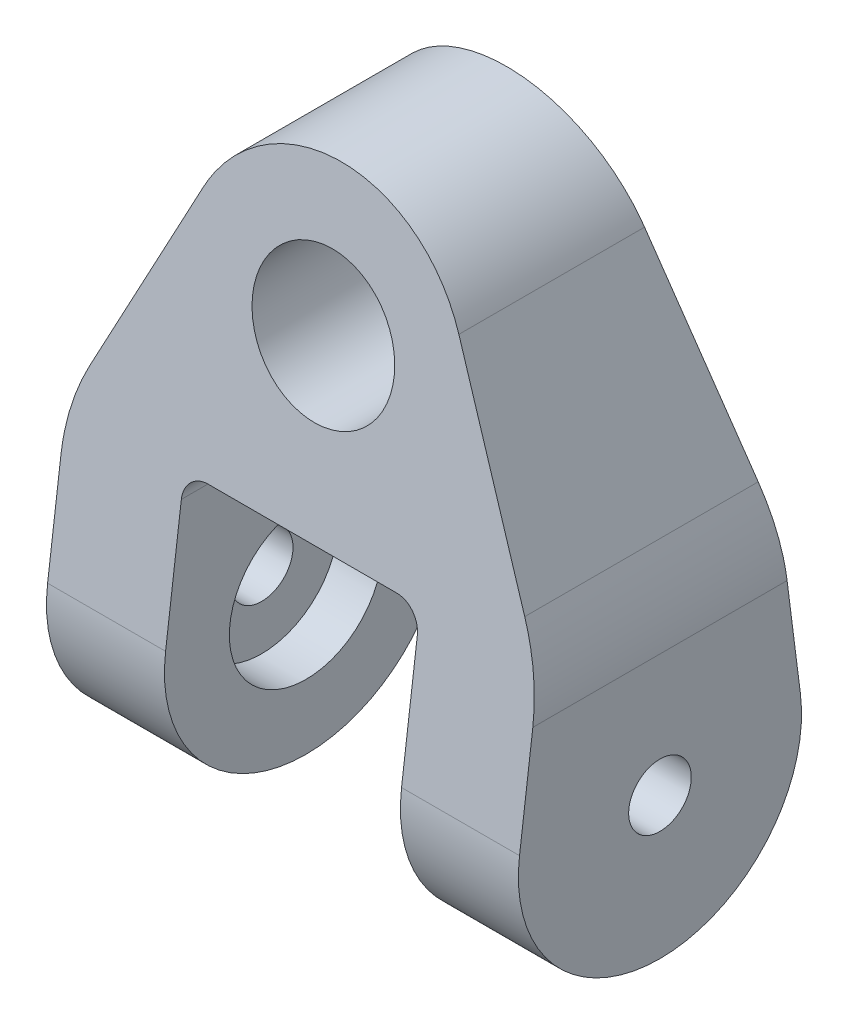
SolidWorks part; units mm, degrees
ref_plane "Front Plane" through (0, 0, 0) normal (0, 0, 1) x (1, 0, 0)
ref_plane "Top Plane" through (0, 0, 0) normal (0, 1, 0) x (1, 0, 0)
ref_plane "Right Plane" through (0, 0, 0) normal (1, 0, 0) x (0, 0, -1)
sketch "Sketch1" plane through (0, 0, 0) normal (0, 0, 1) x (1, 0, 0)
  line L0 (0, 0) -> (0, 44.8572) construction
  line L1 (17.1848, 8.2211) -> (31.75, -22.225)
  line L2 (-17.1848, 8.2211) -> (-31.75, -22.225)
  line L3 (31.75, -22.225) -> (31.75, -63.5)
  line L4 (-31.75, -22.225) -> (-31.75, -63.5)
  line L5 (31.75, -63.5) -> (15.875, -63.5)
  line L6 (-31.75, -63.5) -> (-15.875, -63.5)
  line L7 (15.875, -63.5) -> (15.875, -22.225)
  line L8 (-15.875, -63.5) -> (-15.875, -22.225)
  line L9 (15.875, -22.225) -> (-15.875, -22.225)
  circle A0 centre (0, 0) radius 9.525
  arc A1 (17.1848, 8.2211) -> (-17.1848, 8.2211) centre (0, 0) ccw
  dimension "D1" = 19.05
  dimension "D6" = 19.05
  dimension "D2" = 15.875
  dimension "D3" = 31.75
  dimension "D4" = 41.275
  dimension "D5" = 63.5
extrude "Boss-Extrude1" add sketch "Sketch1" along normal mid plane 38.1
sketch "Sketch2" plane through (0, 0, 0) normal (1, 0, 0) x (0, 0, -1)
  line L0 (0, 0) -> (0, -44.45) construction
  line L1 (18.8972, -42.042) -> (11.1125, 19.05)
  line L2 (19.05, 19.05) -> (-19.05, 19.05) construction
  line L3 (-18.8972, -42.042) -> (-11.1125, 19.05)
  line L4 (11.1125, 19.05) -> (-11.1125, 19.05)
  line L5 (-19.05, -63.5) -> (19.05, -63.5) construction
  line L6 (19.05, -63.5) -> (19.05, -22.225) construction
  arc A0 (-18.8972, -42.042) -> (18.8972, -42.042) centre (0, -44.45) ccw
  dimension "D1" = 22.225
extrude "Cut-Extrude1" cut sketch "Sketch2" against normal mid plane 63.5 flip side to cut
fillet "Fillet1" radius 3.175 2 edges at (-15.875, -22.225, 0) (15.875, -22.225, 0)
fillet "Fillet2" radius 25.4 2 edges at (-31.75, -22.225, 0) (31.75, -22.225, 0)
hole_wizard "CBORE for 5/16 Hex Cap Screw1" positions "Sketch4" profile "Sketch3" counterbore size "5/16" standard "ANSI Inch"
sketch "Sketch4" plane through (-15.875, 0, 0) normal (1, 0, 0) x (0, 0, -1)
  arc A0 (-18.8972, -42.042) -> (18.8972, -42.042) centre (0, -44.45) ccw construction
  point P0 (0, -44.45)
sketch "Sketch3" plane through (-15.875, -44.45, 0) normal (0, 1, 0) x (0, 0, -1)
  line L0 (0, 0) -> (0, 15.875)
  line L1 (0, 15.875) -> (4.2164, 15.875)
  line L3 (4.2164, 15.875) -> (4.2164, 5.969)
  line L4 (4.2164, 5.969) -> (10.3187, 5.969)
  line L5 (10.3187, 5.969) -> (10.3187, 0)
  line L7 (10.3187, 0) -> (0, 0)
  line L11 (0, -6.35) -> (0, 107.95) construction
  dimension "Thru Hole Dia." = 8.4328
  dimension "Thru Hole Depth" = 15.875
  dimension "C'Bore Dia." = 20.6375
  dimension "C'Bore Depth" = 5.969
mirror "Mirror1" about plane through (0, 0, 0) normal (1, 0, 0) of "CBORE for 5/16 Hex Cap Screw1"
